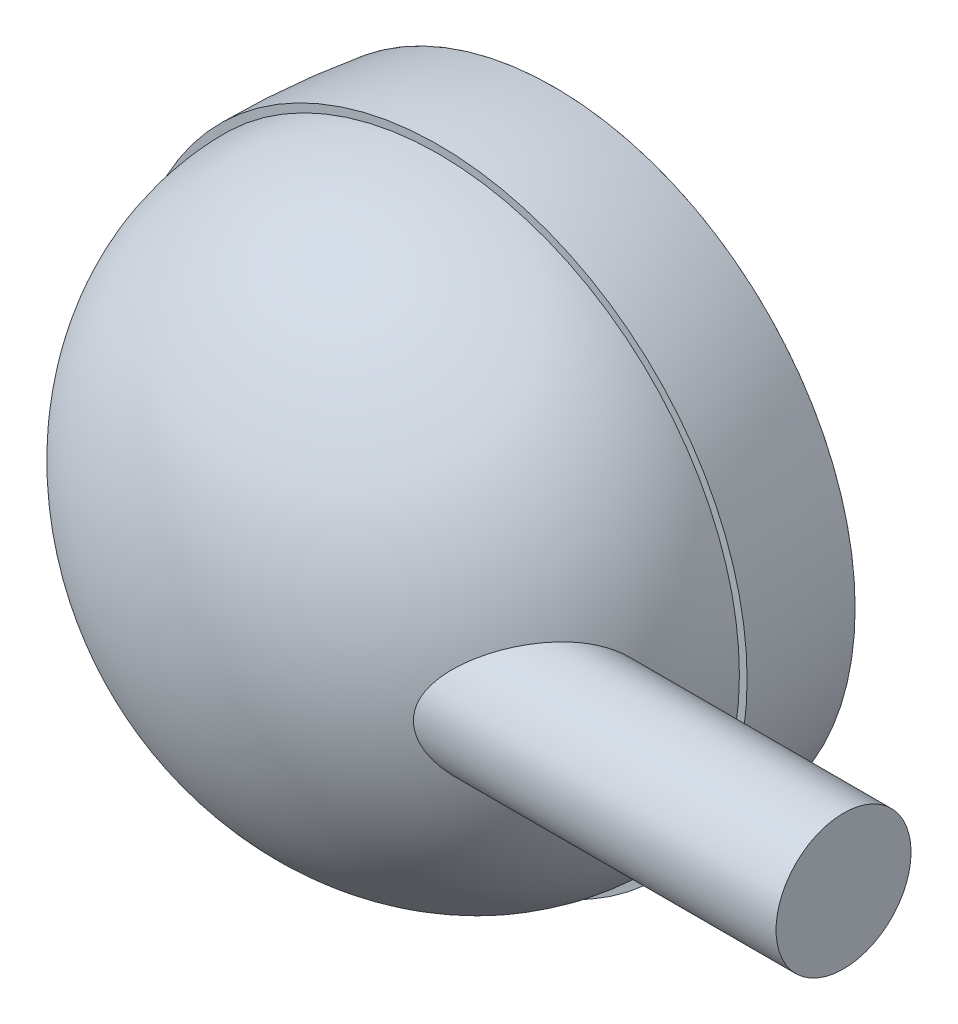
SolidWorks part; units mm, degrees
ref_plane "Front Plane" through (0, 0, 0) normal (0, 0, 1) x (1, 0, 0)
ref_plane "Top Plane" through (0, 0, 0) normal (0, 1, 0) x (1, 0, 0)
ref_plane "Right Plane" through (0, 0, 0) normal (1, 0, 0) x (0, 0, -1)
sketch "Sketch5" plane through (0, 0, -477.5) normal (-1, 0, 0) x (0, 0, 1)
  line L0 (505.5, 75.9617) -> (505.5, 77.9911)
  line L1 (507.5, 78) -> (507.5, 80)
  line L2 (477.5, 78) -> (477.5, 75.982)
  line L3 (570.5, 0) -> (572.5, 0)
  line L4 (477.5, 0) -> (572.5, 0) construction
  line L5 (477.5, 78) -> (477.5, 0) construction
  line L6 (507.5, 80) -> (507.5, 0) construction
  arc A0 (477.5, 78) -> (507.5, 80) centre (507.5, -146) cw
  arc A1 (477.5, 75.982) -> (505.5, 77.9911) centre (507.5, -146) cw
  arc A2 (477.7655, 76.0177) -> (505.5, 77.9911) centre (507.5, -146) cw construction
  ellipse E0 centre (507.5, 0) end of major axis (507.5, -78) minor radius 65 (572.5, 0) -> (507.5, 78) ccw
  spline S0 degree 1 poles (570.5, 0) (505.5, 75.9617) knots 0 0 1 1 construction
  spline S1 degree 3 poles (570.5, 0) (570.5, 5.0807) (569.6459, 15.3006) (565.8569, 29.9598) (559.72, 43.4099) (548.7568, 58.9945) (530.6744, 72.8605) (513.8585, 76.2823) (505.5, 75.9617) knots 1.570796 1.570796 1.570796 1.570796 1.77114 1.971484 2.171828 2.372172 2.772859 3.173547 3.173547 3.173547 3.173547
  dimension "D5" = 2
  dimension "D1" = 30
  dimension "D2" = 95
  dimension "D3" = 80
  dimension "D4" = 2
revolve "Revolve2" add sketch "Sketch5" angle 360 about L4
sketch "Sketch6" plane through (0, 0, 0) normal (1, 0, 0) x (0, 0, -1)
  line L0 (0, 0) -> (15, 0)
  line L1 (0, -78) -> (0, 78) construction
  line L2 (15, 0) -> (15, 28.618) construction
  line L3 (0, 0) -> (0, 78)
  arc A0 (0, 78) -> (15, 0) centre (-195.3, 0) cw
  dimension "D1" = 15
revolve "Revolve3" add sketch "Sketch6" angle 360 about L0
sketch "Sketch7" plane through (0, 0, 0) normal (1, 0, 0) x (0, 0, -1)
  line L0 (-65, 0) -> (0, 0) construction
  line L1 (0, 78) -> (0, -78) construction
  circle A0 centre (-65, 0) radius 17.5
  dimension "D2" = 35
  dimension "D1" = 65
extrude "Boss-Extrude1" add sketch "Sketch7" against normal up to next from offset 140
